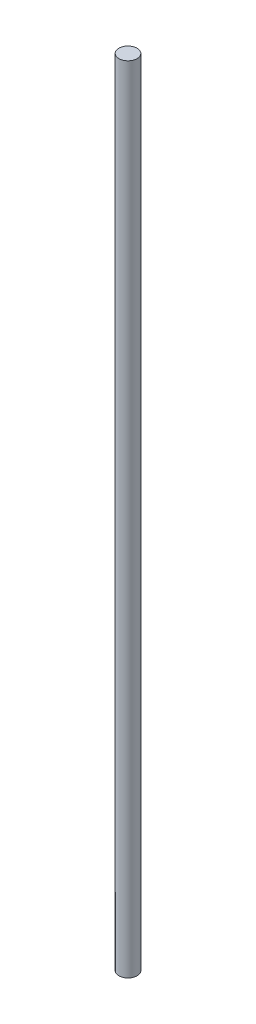
SolidWorks part; units mm, degrees
ref_plane "Front Plane" through (0, 0, 0) normal (0, 0, 1) x (1, 0, 0)
ref_plane "Top Plane" through (0, 0, 0) normal (0, 1, 0) x (1, 0, 0)
ref_plane "Right Plane" through (0, 0, 0) normal (1, 0, 0) x (0, 0, -1)
sketch "Sketch1" plane through (0, 0, 0) normal (0, 1, 0) x (1, 0, 0)
  circle A0 centre (0, 0) radius 4
  dimension "D1" = 8
extrude "Boss-Extrude1" add sketch "Sketch1" along normal blind 350 contours A0
